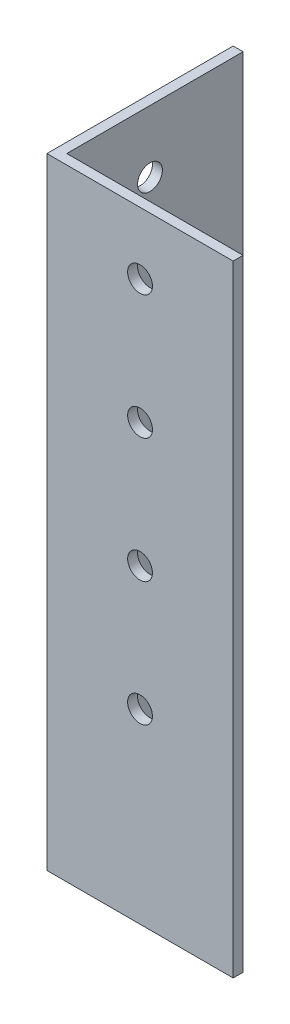
SolidWorks part; units mm, degrees
ref_plane "Спереди" through (0, 0, 0) normal (0, 0, 1) x (1, 0, 0)
ref_plane "Сверху" through (0, 0, 0) normal (0, 1, 0) x (1, 0, 0)
ref_plane "Справа" through (0, 0, 0) normal (1, 0, 0) x (0, 0, -1)
sketch "Эскиз1" plane through (0, 0, 0) normal (0, 1, 0) x (1, 0, 0)
  line L0 (0, 0) -> (75, 0)
  line L1 (0, 0) -> (0, 75)
extrude "Вытянуть-Тонкостенный1" add sketch "Эскиз1" along normal blind 250 thin thin type one direction wall 4
sketch "Эскиз2" plane through (0, 0, 0) normal (0, 0, 1) x (1, 0, 0)
  circle A0 centre (37.5, 225) radius 5
  circle A1 centre (37.5, 175) radius 5
  circle A2 centre (37.5, 125) radius 5
  circle A3 centre (37.5, 75) radius 5
  dimension "D1" = 4
extrude "Вырез-Вытянуть1" cut sketch "Эскиз2" against normal blind 10
sketch "Эскиз3" plane through (0, 0, 0) normal (-1, 0, 0) x (0, 0, 1)
  circle A0 centre (-37.5, 225) radius 5
  circle A1 centre (-37.5, 175) radius 5
  circle A2 centre (-37.5, 125) radius 5
  circle A3 centre (-37.5, 75) radius 5
  dimension "D1" = 4
extrude "Вырез-Вытянуть2" cut sketch "Эскиз3" against normal blind 10
